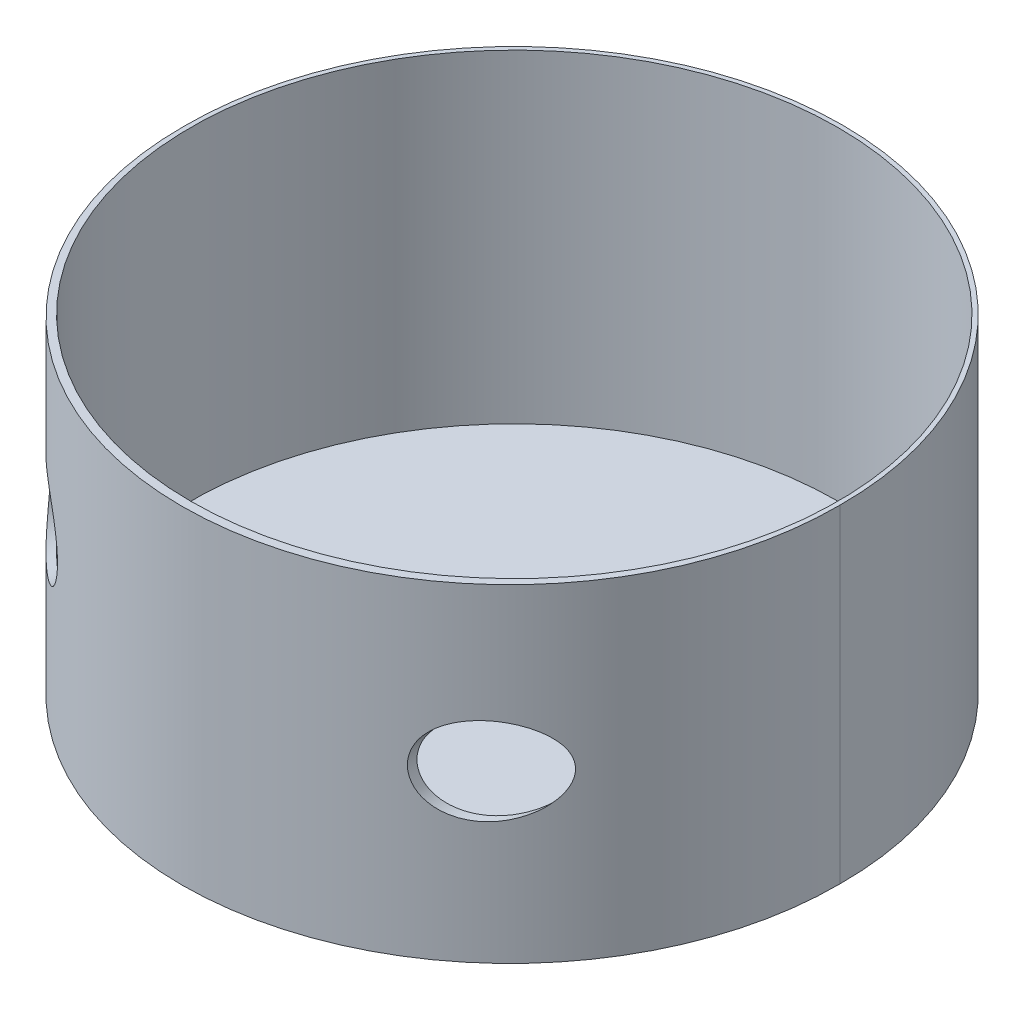
SolidWorks part; units mm, degrees
ref_plane "Plan de face" through (0, 0, 0) normal (0, 0, 1) x (1, 0, 0)
ref_plane "Plan de dessus" through (0, 0, 0) normal (0, 1, 0) x (1, 0, 0)
ref_plane "Plan de droite" through (0, 0, 0) normal (1, 0, 0) x (0, 0, -1)
sketch "Esquisse2" plane through (0, 0, 0) normal (0, 1, 0) x (1, 0, 0)
  circle A0 centre (0, 0) radius 150
  dimension "D1" = 300
extrude "Boss.-Extru.1" add sketch "Esquisse2" along normal blind 150
sketch "Esquisse3" plane through (0, 0, 0) normal (0, 1, 0) x (1, 0, 0)
  circle A0 centre (0, 0) radius 148
extrude "Enlèv. mat.-Extru.1" cut sketch "Esquisse3" along normal blind 148
sketch "Esquisse4" plane through (0, 0, 0) normal (0, 0, 1) x (1, 0, 0)
  line L0 (-150, 150) -> (-150, 0) construction
  line L1 (-150, 150) -> (150, 150) construction
  line L2 (150, 150) -> (150, 0) construction
  line L5 (0, 0) -> (0, 2) construction
  line L6 (-150, 2) -> (150, 2) construction
  dimension "D1" = 2
sketch "Esquisse5" plane through (0, 150, 0) normal (0, 1, 0) x (1, 0, 0)
  line L0 (-150, 0) -> (-150, -2)
  line L1 (-150, 0) -> (150, 0) construction
  line L2 (150, 0) -> (150, -2)
  line L3 (0, 0) -> (0, -2) construction
  circle A0 centre (0, 0) radius 150 construction
  circle A1 centre (0, -2) radius 150
  dimension "D4" = 300
  dimension "D1" = 2
  dimension "D2" = 2
  dimension "D3" = 2
extrude "Boss.-Extru.2" add sketch "Esquisse5" against normal blind 150 contours A1
sketch "Esquisse6" plane through (0, 0, 0) normal (0, 1, 0) x (1, 0, 0)
  circle A0 centre (0, 0) radius 148
  dimension "D1" = 296
extrude "Enlèv. mat.-Extru.2" cut sketch "Esquisse6" along normal blind 177
sketch "Esquisse7" plane through (0, 0, 0) normal (0, -1, 0) x (1, 0, 0)
  line L0 (-150, 0) -> (150, 0) construction
  circle A0 centre (0, 0) radius 148
extrude "Boss.-Extru.3" add sketch "Esquisse7" against normal blind 2
sketch "Esquisse8" plane through (0, 0, 0) normal (0, 1, 0) x (1, 0, 0)
sketch "Esquisse9" plane through (0, 0, 0) normal (0, 0, 1) x (1, 0, 0)
  line L0 (0, 150) -> (0, 0) construction
  line L1 (-150, 150) -> (150, 150) construction
  line L2 (-150, 75) -> (150, 75) construction
  line L5 (-100.4559, 147.0246) -> (-100, 150) construction
  line L6 (-100, 150) -> (-100, 2) construction
  line L7 (-150, 2) -> (150, 2) construction
  line L8 (-150, 150) -> (-150, 0) construction
  line L9 (150, 150) -> (150, 0) construction
  circle A1 centre (-100, 76) radius 20
  circle A2 centre (100, 76) radius 20
  dimension "D2" = 40
  dimension "D1" = 100
extrude "Enlèv. mat.-Extru.3" cut sketch "Esquisse9" along normal blind 200
